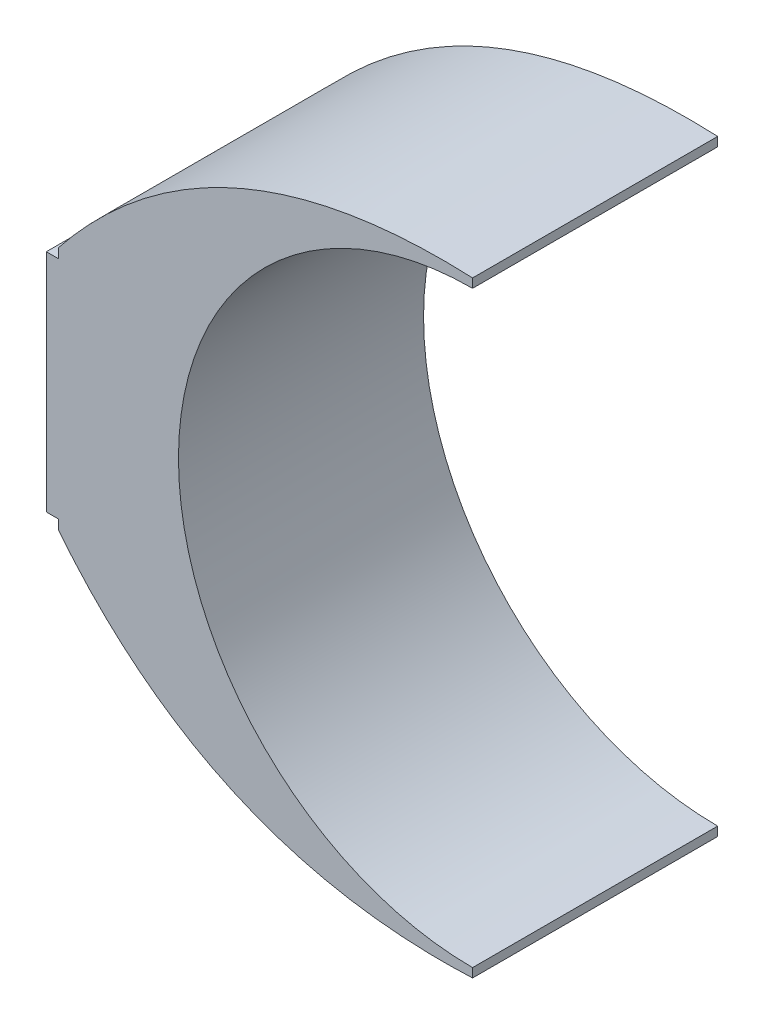
SolidWorks part; units mm, degrees
ref_plane "Front Plane" through (0, 0, 0) normal (0, 0, 1) x (1, 0, 0)
ref_plane "Top Plane" through (0, 0, 0) normal (0, 1, 0) x (1, 0, 0)
ref_plane "Right Plane" through (0, 0, 0) normal (1, 0, 0) x (0, 0, -1)
sketch "Sketch1" plane through (0, 0, 0) normal (0, 0, 1) x (1, 0, 0)
  line L0 (4.115, -0.2963) -> (-1.6711, -0.2963) construction
  line L2 (4.115, 2.1773) -> (4.115, 2.1037)
  line L3 (4.115, -2.7699) -> (4.115, -2.6963)
  line L4 (0.6367, 0.6234) -> (0.6367, -1.2159)
  line L5 (0.6367, -1.2159) -> (0.7367, -1.2159)
  line L6 (0.7367, -1.2159) -> (0.7367, -1.2954)
  line L7 (0.6367, 0.6234) -> (0.7367, 0.6234)
  line L8 (0.7367, 0.6234) -> (0.7367, 0.7029)
  arc A0 (4.115, 2.1037) -> (4.115, -2.6963) centre (4.115, -0.2963) ccw
  spline S0 degree 2 poles (4.115, 2.1773) (1.9866, 2.2734) (0.7367, 0.7029) knots 0 0 0 1 1 1
  spline S3 degree 2 poles (4.115, -2.7699) (1.9866, -2.8659) (0.7367, -1.2954) knots 0 0 0 1 1 1
  dimension "D1" = 4.8
  dimension "D2" = 3.8401
  dimension "D3" = 0.1
extrude "Boss-Extrude1" add sketch "Sketch1" along normal blind 2
